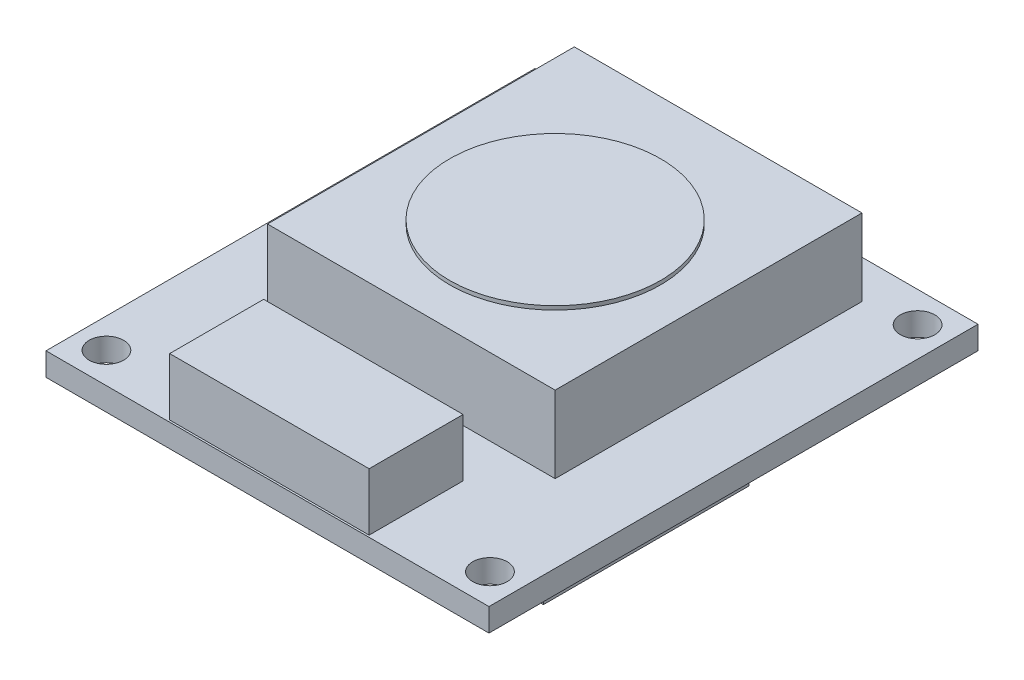
SolidWorks part; units mm, degrees
ref_plane "前视基准面" through (0, 0, 0) normal (0, 0, 1) x (1, 0, 0)
ref_plane "上视基准面" through (0, 0, 0) normal (0, 1, 0) x (1, 0, 0)
ref_plane "右视基准面" through (0, 0, 0) normal (1, 0, 0) x (0, 0, -1)
sketch "草图1" plane through (0, 0, 0) normal (0, 1, 0) x (1, 0, 0)
  line L0 (-20.4578, 0) -> (20.4578, 0) construction
  line L1 (-11.55, -12.75) -> (11.55, -12.75)
  line L2 (-11.55, -12.75) -> (-11.55, 12.75)
  line L3 (-11.55, 12.75) -> (11.55, 12.75)
  line L4 (11.55, -12.75) -> (11.55, 12.75)
  line L5 (-11.55, -12.75) -> (11.55, 12.75) construction
  line L6 (-11.55, 12.75) -> (11.55, -12.75) construction
  line L7 (0, -15.8152) -> (0, 15.8152) construction
  circle A0 centre (10, 11.15) radius 0.9
  circle A1 centre (-10, 11.15) radius 0.9
  circle A2 centre (10, -11.15) radius 0.9
  circle A3 centre (-10, -11.15) radius 0.9
  point P0 (0, 0)
  point P11 (0, 0)
  point P14 (0, 0)
  dimension "D3" = 1.8
  dimension "D1" = 23.1
  dimension "D2" = 25.5
  dimension "D4" = 20
  dimension "D5" = 22.3
extrude "凸台-拉伸1" add sketch "草图1" along normal blind 1.2
sketch "草图2" plane through (0, 1.2, 0) normal (0, 1, 0) x (1, 0, 0)
  line L0 (0, 20.3291) -> (0, -20.3291) construction
  line L1 (11.55, 12.75) -> (-11.55, 12.75) construction
  line L2 (-7.5, 10.75) -> (7.5, 10.75)
  line L3 (-7.5, 10.75) -> (-7.5, -5.25)
  line L4 (-7.5, -5.25) -> (7.5, -5.25)
  line L5 (7.5, 10.75) -> (7.5, -5.25)
  line L6 (-7.5, 10.75) -> (7.5, -5.25) construction
  line L7 (-7.5, -5.25) -> (7.5, 10.75) construction
  point P0 (0, 2.75)
  point P4 (0, 0)
  dimension "D1" = 15
  dimension "D2" = 16
  dimension "D3" = 2
extrude "凸台-拉伸2" add sketch "草图2" along normal blind 4
sketch "草图3" plane through (0, 5.2, 0) normal (0, 1, 0) x (1, 0, 0)
  line L0 (-7.5, -5.25) -> (7.5, -5.25) construction
  line L3 (-7.5, 10.75) -> (-7.5, -5.25) construction
  circle A0 centre (0, 2.25) radius 5.5
  dimension "D1" = 11
  dimension "D2" = 7.5
  dimension "D3" = 7.5
extrude "凸台-拉伸3" add sketch "草图3" along normal blind 0.2
sketch "草图4" plane through (0, 1.2, 0) normal (0, 1, 0) x (1, 0, 0)
  line L0 (0, -0.1029) -> (0, -19.1745) construction
  line L1 (-11.55, -12.75) -> (11.55, -12.75) construction
  line L2 (-5.2, -7.75) -> (5.2, -7.75)
  line L3 (-5.2, -7.75) -> (-5.2, -12.65)
  line L4 (-5.2, -12.65) -> (5.2, -12.65)
  line L5 (5.2, -7.75) -> (5.2, -12.65)
  line L6 (-5.2, -7.75) -> (5.2, -12.65) construction
  line L7 (-5.2, -12.65) -> (5.2, -7.75) construction
  point P2 (0, -10.2)
  dimension "D1" = 10.4
  dimension "D2" = 5
  dimension "D3" = 0.1
extrude "凸台-拉伸4" add sketch "草图4" along normal blind 3
sketch "草图5" plane through (0, 0, 0) normal (0, -1, 0) x (1, 0, 0)
  line L1 (-3.5732, 11.2883) -> (3.5105, 11.2883)
  line L2 (-3.5732, 11.2883) -> (-3.5732, -5.0617)
  line L3 (-3.5732, -5.0617) -> (3.5105, -5.0617)
  line L4 (3.5105, 11.2883) -> (3.5105, -5.0617)
  line L5 (-3.5732, 11.2883) -> (3.5105, -5.0617) construction
  line L6 (-3.5732, -5.0617) -> (3.5105, 11.2883) construction
  line L7 (-3.8109, -8.306) -> (-2.4449, -8.306)
  line L8 (-3.8109, -8.306) -> (-3.8109, -5.9801)
  line L9 (-3.8109, -5.9801) -> (-2.4449, -5.9801)
  line L10 (-2.4449, -8.306) -> (-2.4449, -5.9801)
  line L11 (-3.8109, -8.306) -> (-2.4449, -5.9801) construction
  line L12 (-3.8109, -5.9801) -> (-2.4449, -8.306) construction
  line L13 (6.8646, -2.2116) -> (8.6997, -2.2116)
  line L14 (6.8646, -2.2116) -> (6.8646, -4.1302)
  line L15 (6.8646, -4.1302) -> (8.6997, -4.1302)
  line L16 (8.6997, -2.2116) -> (8.6997, -4.1302)
  line L17 (6.8646, -2.2116) -> (8.6997, -4.1302) construction
  line L18 (6.8646, -4.1302) -> (8.6997, -2.2116) construction
  line L19 (-9.5022, 8.7924) -> (-6.3272, 8.7924)
  line L20 (-9.5022, 8.7924) -> (-9.5022, -4.4777)
  line L21 (-9.5022, -4.4777) -> (-6.3272, -4.4777)
  line L22 (-6.3272, 8.7924) -> (-6.3272, -4.4777)
  line L23 (-9.5022, 8.7924) -> (-6.3272, -4.4777) construction
  line L24 (-9.5022, -4.4777) -> (-6.3272, 8.7924) construction
  line L25 (-10.0842, -6.1262) -> (-5.9732, -6.1262)
  line L26 (-10.0842, -6.1262) -> (-10.0842, -8.1599)
  line L27 (-10.0842, -8.1599) -> (-5.9732, -8.1599)
  line L28 (-5.9732, -6.1262) -> (-5.9732, -8.1599)
  line L29 (-10.0842, -6.1262) -> (-5.9732, -8.1599) construction
  line L30 (-10.0842, -8.1599) -> (-5.9732, -6.1262) construction
  line L37 (4.9356, 9.2456) -> (10.8829, 9.2456)
  line L38 (4.9356, 9.2456) -> (4.9356, -1.4632)
  line L39 (4.9356, -1.4632) -> (10.8829, -1.4632)
  line L40 (10.8829, 9.2456) -> (10.8829, -1.4632)
  line L41 (4.9356, 9.2456) -> (10.8829, -1.4632) construction
  line L42 (4.9356, -1.4632) -> (10.8829, 9.2456) construction
  point P0 (-0.0314, 3.1133)
  point P5 (-3.1279, -7.1431)
  point P10 (7.7821, -3.1709)
  point P15 (-7.9147, 2.1574)
  point P20 (-8.0287, -7.1431)
  point P30 (7.9092, 3.8912)
extrude "凸台-拉伸5" add sketch "草图5" along normal blind 0.8
